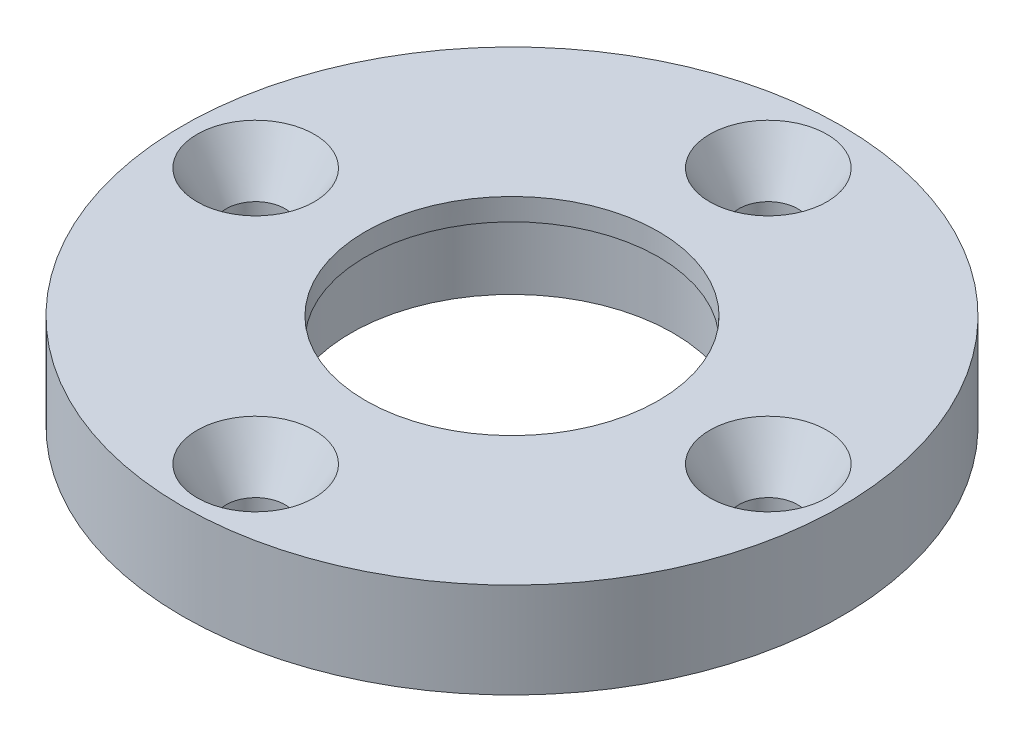
SolidWorks part; units mm, degrees
material "6061 合金"
ref_plane "前视基准面" through (0, 0, 0) normal (0, 0, 1) x (1, 0, 0)
ref_plane "上视基准面" through (0, 0, 0) normal (0, 1, 0) x (1, 0, 0)
ref_plane "右视基准面" through (0, 0, 0) normal (1, 0, 0) x (0, 0, -1)
sketch "草图1" plane through (0, 0, 0) normal (0, 1, 0) x (1, 0, 0)
  circle A0 centre (0, 0) radius 22.5
  circle A1 centre (0, 0) radius 10
  dimension "D1" = 20
  dimension "D2" = 45
extrude "凸台-拉伸1" add sketch "草图1" along normal blind 6.5
sketch "草图2" plane through (0, 6.5, 0) normal (0, 1, 0) x (1, 0, 0)
  circle A0 centre (0, 17.5) radius 2
  circle A1 centre (17.5, 0) radius 2
  circle A2 centre (0, -17.5) radius 2
  circle A3 centre (-17.5, 0) radius 2
  point P12 (0, 0)
  dimension "D1" = 4
  dimension "D2" = 17.5
  dimension "D3" = 4
extrude "切除-拉伸1" cut sketch "草图2" against normal through all
sketch "草图3" plane through (0, 0, 0) normal (0, -1, 0) x (1, 0, 0)
  circle A0 centre (0, 0) radius 11
  dimension "D1" = 22
extrude "切除-拉伸2" cut sketch "草图3" against normal blind 5
chamfer "倒角1" distance 2 distance2 3.4 4 edges at (-17.5, 6.5, 2) (0, 6.5, 19.5) (17.5, 6.5, 2) (0, 6.5, -15.5)
